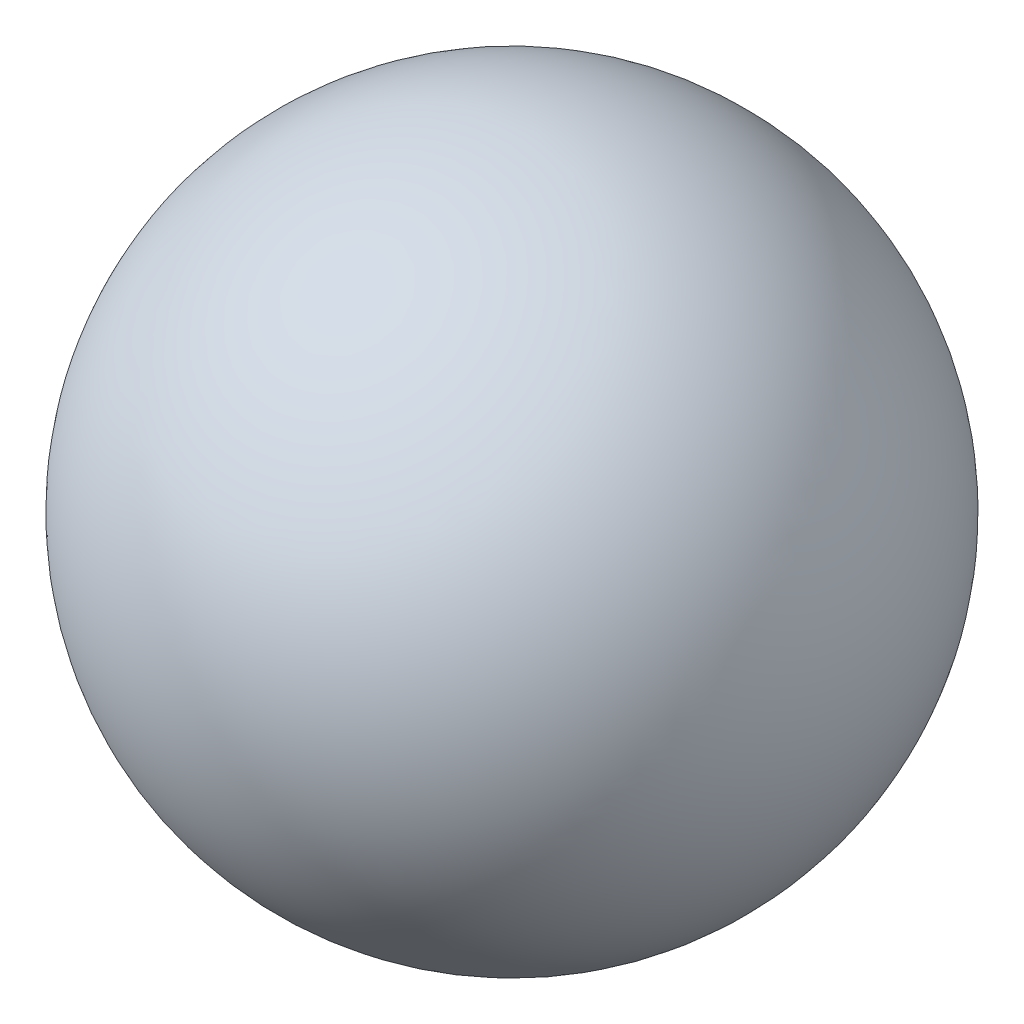
SolidWorks part; units mm, degrees
material "AISI 1035 Acier (SS)"
ref_plane "Plan de face" through (0, 0, 0) normal (0, 0, 1) x (1, 0, 0)
ref_plane "Plan de dessus" through (0, 0, 0) normal (0, 1, 0) x (1, 0, 0)
ref_plane "Plan de droite" through (0, 0, 0) normal (1, 0, 0) x (0, 0, -1)
sketch "Esquisse1" plane through (0, 0, 0) normal (0, 0, 1) x (1, 0, 0)
  line L0 (-40, 0) -> (40, 0)
  arc A0 (-40, 0) -> (40, 0) centre (0, 0) ccw
  dimension "D1" = 40
  dimension "D2" = 80
revolve "Révolution1" add sketch "Esquisse1" angle 360 about L0
